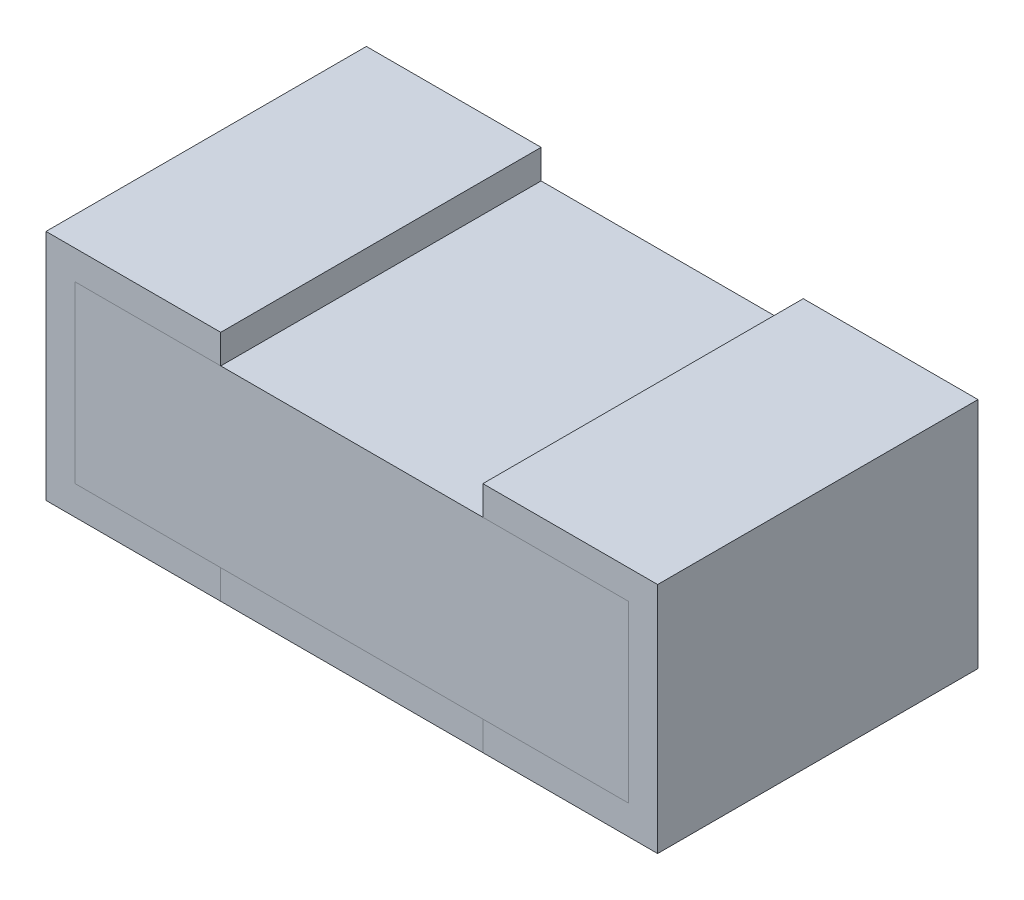
SolidWorks part; units mm, degrees
ref_plane "Front Plane" through (0, 0, 0) normal (0, 0, 1) x (1, 0, 0)
ref_plane "Top Plane" through (0, 0, 0) normal (0, 1, 0) x (1, 0, 0)
ref_plane "Right Plane" through (0, 0, 0) normal (1, 0, 0) x (0, 0, -1)
sketch "Szkic1" plane through (0, 0, 0) normal (0, 0, 1) x (1, 0, 0)
  line L0 (0.3, 0.05) -> (0.05, 0.05)
  line L1 (0.05, 0.05) -> (0.05, 0.35)
  line L2 (0.05, 0.35) -> (0.3, 0.35)
  line L3 (0.3, 0.35) -> (0.3, 0.4)
  line L4 (0.3, 0.4) -> (0, 0.4)
  line L5 (0, 0.4) -> (0, 0)
  line L6 (0, 0) -> (0.3, 0)
  line L7 (0.3, 0) -> (0.3, 0.05)
  line L11 (0.75, 0.35) -> (1, 0.35)
  line L12 (1, 0.35) -> (1, 0.05)
  line L13 (1, 0.05) -> (0.75, 0.05)
  line L14 (0.75, 0.05) -> (0.75, 0)
  line L15 (0.75, 0) -> (1.05, 0)
  line L16 (1.05, 0) -> (1.05, 0.4)
  line L17 (1.05, 0.4) -> (0.75, 0.4)
  line L18 (0.75, 0.4) -> (0.75, 0.35)
extrude "Dodanie-wyciągnięcie1" add sketch "Szkic1" along normal blind 0.55
sketch "Szkic2" plane through (0, 0, 0.55) normal (0, 0, 1) x (1, 0, 0)
  line L0 (0.75, 0) -> (0.3, 0)
  line L1 (0.3, 0) -> (0.3, 0.05)
  line L2 (0.3, 0.05) -> (0.75, 0.05)
  line L3 (0.75, 0.05) -> (0.75, 0)
extrude "Dodanie-wyciągnięcie2" add sketch "Szkic2" against normal blind 0.55 separate body
sketch "Szkic3" plane through (0, 0, 0.55) normal (0, 0, 1) x (1, 0, 0)
  line L0 (1, 0.05) -> (0.05, 0.05)
  line L1 (0.05, 0.05) -> (0.05, 0.35) construction
  line L2 (0.05, 0.05) -> (0.05, 0.35)
  line L3 (0.05, 0.35) -> (1, 0.35)
  line L4 (1, 0.35) -> (1, 0.05)
extrude "Dodanie-wyciągnięcie3" add sketch "Szkic3" against normal blind 0.55 separate body
